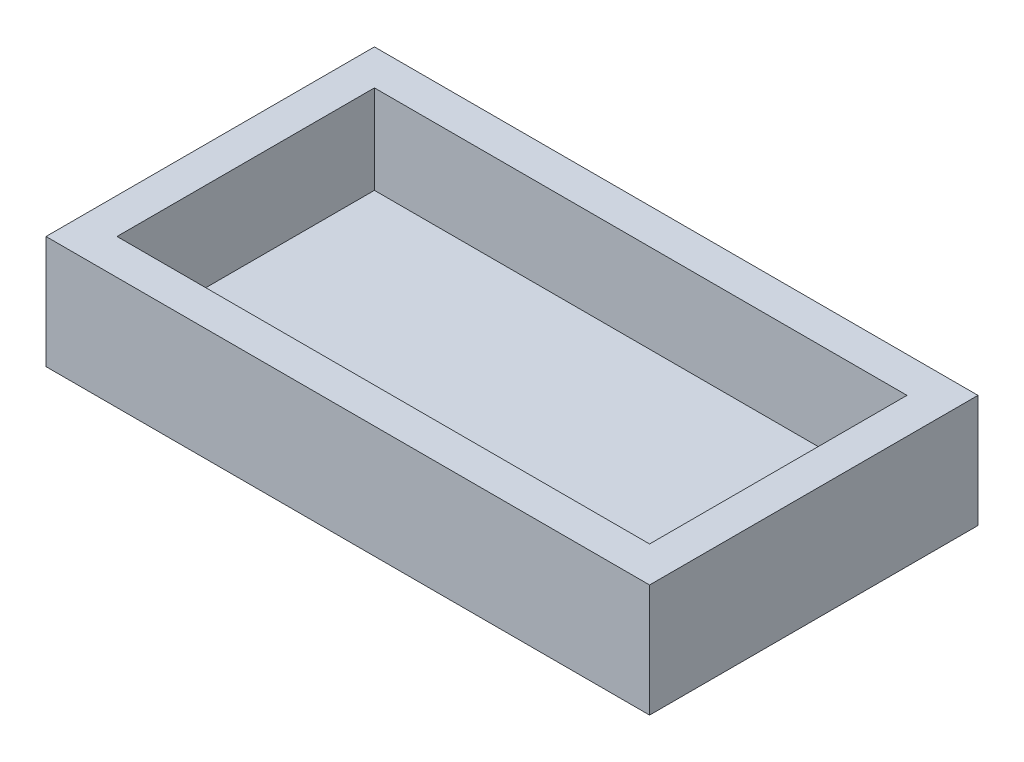
SolidWorks part; units mm, degrees
ref_plane "Front Plane" through (0, 0, 0) normal (0, 0, 1) x (1, 0, 0)
ref_plane "Top Plane" through (0, 0, 0) normal (0, 1, 0) x (1, 0, 0)
ref_plane "Right Plane" through (0, 0, 0) normal (1, 0, 0) x (0, 0, -1)
sketch "Sketch1" plane through (0, 0, 0) normal (0, 1, 0) x (1, 0, 0)
  line L0 (-2, -2) -> (-2, 16.5)
  line L1 (0, 0) -> (30, 0)
  line L2 (0, 0) -> (0, 14.5)
  line L3 (0, 14.5) -> (30, 14.5)
  line L4 (30, 0) -> (30, 14.5)
  line L5 (0, 0) -> (30, 14.5) construction
  line L6 (0, 14.5) -> (30, 0) construction
  line L7 (-2, 16.5) -> (32, 16.5)
  line L8 (32, -2) -> (32, 16.5)
  line L9 (-2, -2) -> (32, -2)
  point P0 (15, 7.25)
  point P5 (0, 0)
  dimension "D1" = 14.5
  dimension "D2" = 30
  dimension "D3" = 2
extrude "Boss-Extrude1" add sketch "Sketch1" along normal blind 6.35 contours L0 L7 L8 L9
sketch "Sketch2" plane through (0, 0, 0) normal (0, 1, 0) x (1, 0, 0)
  line L1 (0, 0) -> (30, 0)
  line L2 (0, 0) -> (0, 14.5)
  line L3 (0, 14.5) -> (30, 14.5)
  line L4 (30, 0) -> (30, 14.5)
  line L5 (0, 0) -> (30, 14.5) construction
  line L6 (0, 14.5) -> (30, 0) construction
  point P0 (15, 7.25)
  point P5 (0, 0)
  dimension "D1" = 14.5
  dimension "D2" = 30
extrude "Boss-Extrude3" add sketch "Sketch2" along normal blind 1.35
